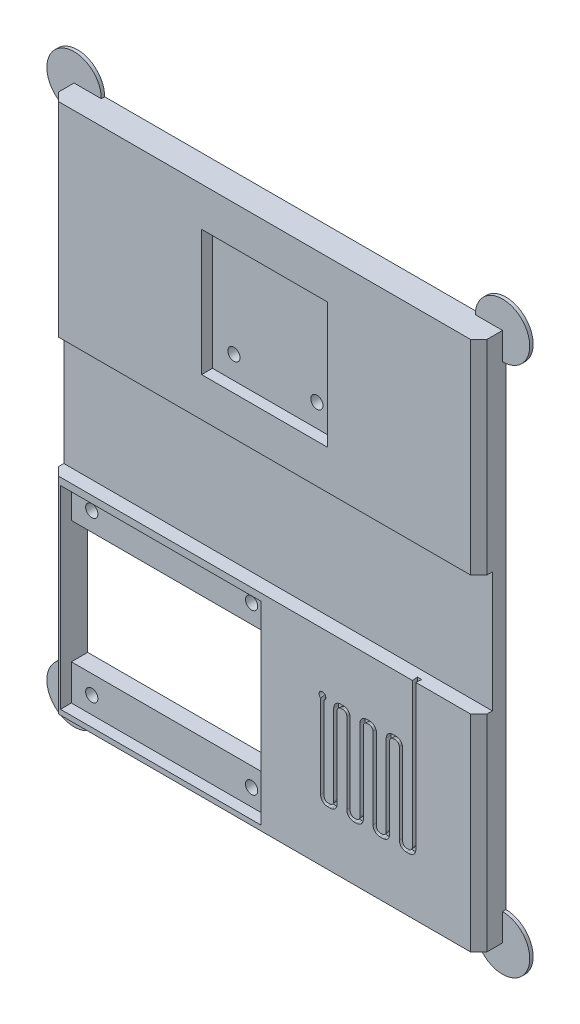
SolidWorks part; units mm, degrees
ref_plane "Front Plane" through (0, 0, 0) normal (0, 0, 1) x (1, 0, 0)
ref_plane "Top Plane" through (0, 0, 0) normal (0, 1, 0) x (1, 0, 0)
ref_plane "Right Plane" through (0, 0, 0) normal (1, 0, 0) x (0, 0, -1)
sketch "Sketch2" [suppressed] plane through (0, 0, 0) normal (0, 0, 1) x (1, 0, 0)
  line L0 (9.8069, 1.0971) -> (9.8069, -3.1704) construction
  line L1 (6.8551, -5.1618) -> (6.8551, -16.1618) construction
  line L2 (6.8551, -16.1618) -> (16.3814, -10.6618) construction
  line L3 (16.3814, -10.6618) -> (6.8551, -5.1618) construction
  line L4 (6.8551, -10.6618) -> (2.6647, -10.6618) construction
  line L5 (9.5069, 1.0971) -> (9.5069, -2.443)
  line L6 (6.5551, -6.3743) -> (6.5551, -9.8618)
  line L7 (8.0551, -15.8154) -> (15.4814, -11.5279)
  line L8 (15.4814, -9.7958) -> (8.0551, -5.5082)
  line L9 (6.0551, -10.3618) -> (3.5127, -10.3618)
  line L10 (10.1069, 1.0971) -> (10.1069, -2.3736)
  line L11 (7.1551, -6.5475) -> (7.1551, -14.7762)
  line L12 (7.9051, -15.2092) -> (15.0314, -11.0948)
  line L13 (15.0314, -10.2288) -> (7.9051, -6.1145)
  line L14 (6.0551, -10.9618) -> (3.5127, -10.9618)
  line L15 (9.5069, 1.0971) -> (9.5069, -3.1704) construction
  line L16 (10.1069, 1.0971) -> (10.1069, -3.1704) construction
  line L17 (6.8551, -10.9618) -> (2.6647, -10.9618) construction
  line L18 (6.8551, -10.3618) -> (2.6647, -10.3618) construction
  line L19 (6.5551, -11.4618) -> (6.5551, -14.9494)
  line L20 (6.5551, -4.6422) -> (6.5551, -16.6814) construction
  line L21 (7.1551, -15.6422) -> (15.7814, -10.6618) construction
  line L22 (15.7814, -10.6618) -> (7.1551, -5.6814) construction
  line L23 (7.1551, -5.6814) -> (7.1551, -15.6422) construction
  line L24 (6.5551, -16.6814) -> (16.9814, -10.6618) construction
  line L25 (16.9814, -10.6618) -> (6.5551, -4.6422) construction
  circle A0 centre (10.1647, -10.6618) radius 7.5 construction
  arc A1 (9.0767, -2.9381) -> (10.5803, -2.8729) centre (10.1647, -10.6618) ccw
  arc A2 (3.0162, -11.5215) -> (3.0162, -9.8021) centre (10.1647, -10.6618) ccw
  arc A3 (9.5069, 1.0971) -> (10.1069, 1.0971) centre (9.8069, 1.0971) cw
  circle A7 centre (10.1647, -10.6618) radius 7.8 construction
  circle A8 centre (10.1647, -10.6618) radius 7.2 construction
  arc A9 (10.1069, -2.3736) -> (10.5803, -2.8729) centre (10.6069, -2.3736) ccw
  arc A10 (9.5069, -2.443) -> (9.0767, -2.9381) centre (9.0069, -2.443) cw
  arc A11 (3.5127, -10.3618) -> (3.0162, -9.8021) centre (3.5127, -9.8618) cw
  arc A12 (3.5127, -10.9618) -> (3.0162, -11.5215) centre (3.5127, -11.4618) ccw
  arc A13 (6.0551, -10.3618) -> (6.5551, -9.8618) centre (6.0551, -9.8618) ccw
  arc A14 (6.5551, -11.4618) -> (6.0551, -10.9618) centre (6.0551, -11.4618) ccw
  arc A15 (15.0314, -11.0948) -> (15.0314, -10.2288) centre (14.7814, -10.6618) ccw
  arc A16 (7.1551, -14.7762) -> (7.9051, -15.2092) centre (7.6551, -14.7762) ccw
  arc A17 (7.1551, -6.5475) -> (7.9051, -6.1145) centre (7.6551, -6.5475) cw
  arc A18 (15.4814, -11.5279) -> (15.4814, -9.7958) centre (14.9814, -10.6618) ccw
  arc A19 (6.5551, -14.9494) -> (8.0551, -15.8154) centre (7.5551, -14.9494) ccw
  arc A20 (6.5551, -6.3743) -> (8.0551, -5.5082) centre (7.5551, -6.3743) cw
  point P12 (6.8551, -10.6618)
  dimension "D2" = 15
  dimension "D3" = 0.5
  dimension "D4" = 1
  dimension "D1" = 11
sketch "Sketch5" plane through (0, 0, 0) normal (0, 0, 1) x (1, 0, 0)
  line L1 (-31.5, 48) -> (31.5, 48)
  line L2 (-31.5, 48) -> (-31.5, -30)
  line L3 (-31.5, -30) -> (31.5, -30)
  line L4 (31.5, 48) -> (31.5, -30)
  point P4 (0, 48)
  dimension "D1" = 63
  dimension "D2" = 30
  dimension "D3" = 48
extrude "Boss-Extrude2" add sketch "Sketch5" along normal blind 4
sketch "Sketch1" plane through (0, 0, 4) normal (0, 0, 1) x (1, 0, 0)
  line L1 (-31, 17.6) -> (31, 17.6) construction
  line L2 (-31, 17.6) -> (-31, 0) construction
  line L3 (-31, 0) -> (31, 0) construction
  line L4 (31, 17.6) -> (31, 0) construction
  line L5 (-9.1, 41.514) -> (9.1, 41.514) construction
  line L6 (-9.1, 41.514) -> (-9.1, 24.114) construction
  line L7 (-9.1, 24.114) -> (9.1, 24.114) construction
  line L8 (9.1, 41.514) -> (9.1, 24.114) construction
  line L9 (-30.1379, -1.3413) -> (-1.1379, -1.3413) construction
  line L10 (-30.1379, -1.3413) -> (-30.1379, -28.8413) construction
  line L11 (-30.1379, -28.8413) -> (-1.1379, -28.8413) construction
  line L12 (-1.1379, -1.3413) -> (-1.1379, -28.8413) construction
  line L13 (-27.6379, -7.8413) -> (-3.6379, -7.8413) construction
  line L14 (-27.6379, -7.8413) -> (-27.6379, -22.8413) construction
  line L15 (-27.6379, -22.8413) -> (-3.6379, -22.8413) construction
  line L16 (-3.6379, -7.8413) -> (-3.6379, -22.8413) construction
  line L17 (0, 37.0153) -> (0, 31.2479) construction
  point P4 (0, 17.6)
  point P18 (0, 0)
  point P20 (-26.7166, -26.6413)
  point P21 (-3.2166, -26.6413)
  point P22 (-3.2166, -4.0013)
  point P23 (-26.7166, -3.1413)
  point P26 (6.1, 27.114)
  point P27 (0, 41.514)
  point P30 (-6.1, 27.114)
  point P32 (-15.6379, -7.8413)
  point P33 (-15.6379, -28.8413)
  dimension "D1" = 17.6
  dimension "D2" = 18.2
  dimension "D3" = 17.4
  dimension "D4" = 27.5
  dimension "D5" = 29
  dimension "D6" = 15
  dimension "D7" = 24
  dimension "D8" = 6
  dimension "D9" = 23.5
  dimension "D10" = 23.5
  dimension "D11" = 12.2
  dimension "D12" = 3
  dimension "D13" = 62
  dimension "D14" = 1.8
sketch "Pause" plane through (0, 0, 4) normal (0, 0, 1) x (1, 0, 0)
  line L0 (19.5, -1.8962) -> (19.5, -8.6557) construction
  line L1 (12.5, -10.5) -> (12.5, -19.5) construction
  line L2 (18.5, -10.5) -> (18.5, -19.5) construction
  line L3 (8, -15) -> (12.5, -15) construction
  line L4 (18.5, -15) -> (23, -15) construction
  line L5 (12.5, -10.5) -> (14.5, -10.5) construction
  line L6 (14.5, -10.5) -> (14.5, -19.5) construction
  line L7 (14.5, -19.5) -> (12.5, -19.5) construction
  line L8 (18.5, -10.5) -> (16.5, -10.5) construction
  line L9 (16.5, -10.5) -> (16.5, -19.5) construction
  line L10 (16.5, -19.5) -> (18.5, -19.5) construction
  line L11 (19.2, -1.8962) -> (19.2, -7.3417)
  line L12 (12.2, -10.9) -> (12.2, -14.2)
  line L13 (14.1, -19.8) -> (12.9, -19.8)
  line L14 (14.8, -10.9) -> (14.8, -19.1)
  line L15 (12.9, -10.2) -> (14.1, -10.2)
  line L16 (18.8, -10.9) -> (18.8, -14.2)
  line L17 (16.9, -19.8) -> (18.1, -19.8)
  line L18 (16.2, -10.9) -> (16.2, -19.1)
  line L19 (18.1, -10.2) -> (16.9, -10.2)
  line L20 (8, -15.3) -> (8.006, -15.3)
  line L21 (19.3, -15.3) -> (22.1521, -15.3)
  line L22 (19.8, -1.8962) -> (19.8, -8.2287)
  line L23 (12.8, -11.3) -> (12.8, -18.7)
  line L24 (13.7, -19.2) -> (13.3, -19.2)
  line L25 (14.2, -11.3) -> (14.2, -18.7)
  line L26 (13.3, -10.8) -> (13.7, -10.8)
  line L27 (18.2, -11.3) -> (18.2, -18.7)
  line L28 (17.3, -19.2) -> (17.7, -19.2)
  line L29 (16.8, -11.3) -> (16.8, -18.7)
  line L30 (17.7, -10.8) -> (17.3, -10.8)
  line L31 (8, -14.7) -> (8.006, -14.7)
  line L32 (19.3, -14.7) -> (22.1521, -14.7)
  line L33 (19.2, -1.8962) -> (19.2, -8.6557) construction
  line L34 (8.8479, -15.3) -> (11.7, -15.3)
  line L35 (19.8, -1.8962) -> (19.8, -8.6557) construction
  line L36 (8, -15.3) -> (12.5, -15.3) construction
  line L37 (8.8479, -14.7) -> (11.7, -14.7)
  line L38 (8, -14.7) -> (12.5, -14.7) construction
  line L39 (12.2, -15.8) -> (12.2, -19.1)
  line L40 (12.2, -10.2) -> (12.2, -19.8) construction
  line L41 (18.5, -14.7) -> (23, -14.7) construction
  line L42 (18.8, -15.8) -> (18.8, -19.1)
  line L43 (18.8, -10.2) -> (18.8, -19.8) construction
  line L44 (18.5, -15.3) -> (23, -15.3) construction
  line L45 (22.994, -14.7) -> (23, -14.7)
  line L46 (22.994, -15.3) -> (23, -15.3)
  line L47 (16.8, -19.2) -> (18.2, -19.2) construction
  line L48 (16.8, -10.8) -> (16.8, -19.2) construction
  line L49 (18.2, -10.8) -> (18.2, -19.2) construction
  line L50 (18.2, -10.8) -> (16.8, -10.8) construction
  line L51 (12.8, -10.8) -> (12.8, -19.2) construction
  line L52 (14.2, -19.2) -> (12.8, -19.2) construction
  line L53 (14.2, -10.8) -> (14.2, -19.2) construction
  line L54 (12.8, -10.8) -> (14.2, -10.8) construction
  line L55 (16.2, -10.2) -> (16.2, -19.8) construction
  line L56 (18.8, -10.2) -> (16.2, -10.2) construction
  line L57 (16.2, -19.8) -> (18.8, -19.8) construction
  line L58 (14.8, -19.8) -> (12.2, -19.8) construction
  line L59 (14.8, -10.2) -> (14.8, -19.8) construction
  line L60 (12.2, -10.2) -> (14.8, -10.2) construction
  line L61 (19.5, -1.8962) -> (19.5, -8.6557) construction
  line L62 (31.5, -30) -> (31.5, 48) construction
  line L64 (-31.5, -30) -> (31.5, -30) construction
  line L65 (19.8, -1.8962) -> (19.2, -1.8962)
  circle A0 centre (15.5, -15) radius 7.5 construction
  arc A2 (18.5072, -7.803) -> (20.0108, -8.6366) centre (15.5, -15) ccw
  arc A3 (8.3515, -15.8597) -> (22.6485, -15.8597) centre (15.5, -15) ccw
  circle A4 centre (15.5, -15) radius 7.8 construction
  circle A5 centre (15.5, -15) radius 7.2 construction
  arc A6 (22.6485, -14.1403) -> (8.3515, -14.1403) centre (15.5, -15) ccw
  arc A7 (19.2, -7.3417) -> (18.5072, -7.803) centre (18.7, -7.3417) cw
  arc A8 (20.0108, -8.6366) -> (19.8, -8.2287) centre (20.3, -8.2287) cw
  arc A9 (8.8479, -15.3) -> (8.3515, -15.8597) centre (8.8479, -15.8) ccw
  arc A10 (8.8479, -14.7) -> (8.3515, -14.1403) centre (8.8479, -14.2) cw
  arc A11 (22.1521, -14.7) -> (22.6485, -14.1403) centre (22.1521, -14.2) ccw
  arc A12 (22.6485, -15.8597) -> (22.1521, -15.3) centre (22.1521, -15.8) ccw
  arc A13 (19.3, -14.7) -> (18.8, -14.2) centre (19.3, -14.2) cw
  arc A14 (19.3, -15.3) -> (18.8, -15.8) centre (19.3, -15.8) ccw
  arc A15 (12.2, -15.8) -> (11.7, -15.3) centre (11.7, -15.8) ccw
  arc A16 (11.7, -14.7) -> (12.2, -14.2) centre (11.7, -14.2) ccw
  arc A17 (17.3, -19.2) -> (16.8, -18.7) centre (17.3, -18.7) cw
  arc A18 (18.2, -18.7) -> (17.7, -19.2) centre (17.7, -18.7) cw
  arc A19 (18.2, -11.3) -> (17.7, -10.8) centre (17.7, -11.3) ccw
  arc A20 (16.8, -11.3) -> (17.3, -10.8) centre (17.3, -11.3) cw
  arc A21 (12.8, -18.7) -> (13.3, -19.2) centre (13.3, -18.7) ccw
  arc A22 (13.7, -19.2) -> (14.2, -18.7) centre (13.7, -18.7) ccw
  arc A23 (14.2, -11.3) -> (13.7, -10.8) centre (13.7, -11.3) ccw
  arc A24 (12.8, -11.3) -> (13.3, -10.8) centre (13.3, -11.3) cw
  arc A25 (16.2, -10.9) -> (16.9, -10.2) centre (16.9, -10.9) cw
  arc A26 (18.8, -10.9) -> (18.1, -10.2) centre (18.1, -10.9) ccw
  arc A27 (18.8, -19.1) -> (18.1, -19.8) centre (18.1, -19.1) cw
  arc A28 (16.9, -19.8) -> (16.2, -19.1) centre (16.9, -19.1) cw
  arc A29 (12.2, -19.1) -> (12.9, -19.8) centre (12.9, -19.1) ccw
  arc A30 (14.1, -19.8) -> (14.8, -19.1) centre (14.1, -19.1) ccw
  arc A31 (14.8, -10.9) -> (14.1, -10.2) centre (14.1, -10.9) ccw
  arc A32 (12.2, -10.9) -> (12.9, -10.2) centre (12.9, -10.9) cw
  point P18 (12.5, -15)
  point P73 (22.6937, -14.7)
  dimension "D5" = 15
  dimension "D6" = 0.5
  dimension "D7" = 0.7
  dimension "D1" = 2
  dimension "D2" = 2
  dimension "D3" = 2
  dimension "D4" = 9
  dimension "D8" = 12
  dimension "D9" = 16
  dimension "D10" = 15
  dimension "D11" = 0.3
  dimension "D12" = 0.3
extrude "Cut-Extrude1" [suppressed] cut sketch "Pause" against normal blind 2
sketch "Teensy" plane through (0, 0, 4) normal (0, 0, 1) x (1, 0, 0)
  line L0 (-31.5, 48) -> (-31.5, -30) construction
  line L1 (-31.5, 18) -> (31.5, 18)
  line L2 (-31.5, 18) -> (-31.5, 0.3)
  line L3 (-31.5, 0.3) -> (31.5, 0.3)
  line L4 (31.5, 18) -> (31.5, 0.3)
  line L5 (31.5, -30) -> (31.5, 48) construction
  line L6 (31.5, 48) -> (-31.5, 48) construction
  dimension "D1" = 17.7
  dimension "D2" = 30
extrude "Cut-Extrude3" cut sketch "Teensy" against normal blind 2
sketch "Sketch7" plane through (0, 0, 4) normal (0, 0, 1) x (1, 0, 0)
  line L1 (-9.25, 42.25) -> (9.25, 42.25)
  line L2 (-9.25, 42.25) -> (-9.25, 23.75)
  line L3 (-9.25, 23.75) -> (9.25, 23.75)
  line L4 (9.25, 42.25) -> (9.25, 23.75)
  line L5 (31.5, 48) -> (-31.5, 48) construction
  point P4 (0, 42.25)
  point P5 (-9.25, 33)
  dimension "D1" = 18.5
  dimension "D2" = 18.5
  dimension "D3" = 15
extrude "Cut-Extrude4" cut sketch "Sketch7" against normal blind 1.6
sketch "Sketch8" plane through (0, 0, 4) normal (0, 0, 1) x (1, 0, 0)
  line L0 (-31.5, -30) -> (31.5, -30) construction
  line L1 (-30, -0.75) -> (-0.5, -0.75)
  line L2 (-30, -0.75) -> (-30, -29.25)
  line L3 (-30, -29.25) -> (-0.5, -29.25)
  line L4 (-0.5, -0.75) -> (-0.5, -29.25)
  line L5 (-31.5, 0.3) -> (-31.5, -30) construction
  point P4 (-30, -15)
  dimension "D1" = 29.5
  dimension "D2" = 28.5
  dimension "D3" = 15
  dimension "D4" = 1.5
extrude "Cut-Extrude5" cut sketch "Sketch8" against normal blind 1.6
sketch "Sketch9" plane through (0, 0, 2.4) normal (0, 0, 1) x (1, 0, 0)
  line L0 (-30, -0.75) -> (-30, -29.25) construction
  line L1 (-30, -6) -> (-1, -6)
  line L2 (-30, -6) -> (-30, -24)
  line L3 (-30, -24) -> (-1, -24)
  line L4 (-1, -6) -> (-1, -24)
  line L5 (-0.5, -0.75) -> (-30, -0.75) construction
  line L6 (-15.25, -0.75) -> (-15.25, -29.25) construction
  line L7 (-18.021, -15) -> (-12.479, -15) construction
  line L8 (-30, -29.25) -> (-0.5, -29.25) construction
  circle A0 centre (-27, -3.25) radius 0.9
  circle A1 centre (-3.5, -3.25) radius 0.9
  circle A2 centre (-3.5, -26.75) radius 0.9
  circle A3 centre (-27, -26.75) radius 0.9
  circle A4 centre (-6.1, 27.114) radius 0.9
  circle A5 centre (6.1, 27.114) radius 0.9
  point P23 (-15.25, -15)
  dimension "D4" = 1.8
  dimension "D1" = 29
  dimension "D2" = 18
  dimension "D5" = 23.5
  dimension "D6" = 23.5
extrude "Cut-Extrude6" cut sketch "Sketch9" against normal through all
sketch "Sketch10" plane through (0, 0, 0) normal (0, 0, -1) x (-1, 0, 0)
  circle A0 centre (31.5, 48) radius 4
  circle A1 centre (-31.5, 48) radius 4
  circle A2 centre (-31.5, -30) radius 4
  circle A3 centre (31.5, -30) radius 4
  dimension "D1" = 8
extrude "Boss-Extrude3" add sketch "Sketch10" against normal blind 0.5
sketch "Sketch11" plane through (0, 0, 4) normal (0, 0, 1) x (1, 0, 0)
  line L0 (-31.5, 48) -> (-31.5, 18) construction
  line L1 (-28.5, 42) -> (-28.1, 42)
  line L2 (-28.5, 42) -> (-28.5, 12)
  line L3 (-28.5, 12) -> (-28.1, 12)
  line L4 (-28.1, 42) -> (-28.1, 12)
  line L5 (-25.5, 42) -> (-24.9, 42)
  line L6 (-25.5, 42) -> (-25.5, 12)
  line L7 (-25.5, 12) -> (-24.9, 12)
  line L8 (-24.9, 42) -> (-24.9, 12)
  line L9 (-22.5, 42) -> (-21.7, 42)
  line L10 (-22.5, 42) -> (-22.5, 12)
  line L11 (-22.5, 12) -> (-21.7, 12)
  line L12 (-21.7, 42) -> (-21.7, 12)
  line L13 (31.5, 48) -> (-31.5, 48) construction
  dimension "D1" = 30
  dimension "D2" = 3
  dimension "D3" = 3
  dimension "D4" = 3
  dimension "D5" = 0.4
  dimension "D6" = 0.6
  dimension "D7" = 0.8
  dimension "D8" = 6
extrude "Cut-Extrude7" [suppressed] cut sketch "Sketch11" against normal blind 2 draft 5
chamfer "Chamfer2" distance 1.2 angle 45 4 edges at (-31.5, -14.85, 4) (31.5, -14.85, 4) (31.5, 33, 4) (-31.5, 33, 4)
sketch "Sketch12" plane through (0, 0, 4) normal (0, 0, 1) x (1, 0, 0)
  line L0 (22, 0.3) -> (22, -21.75) construction
  line L1 (22, -21.75) -> (20.0714, -21.75) construction
  line L2 (20.0714, -21.75) -> (20.0714, -8.25) construction
  line L3 (20.0714, -8.25) -> (18.1429, -8.25) construction
  line L4 (18.1429, -8.25) -> (18.1429, -21.75) construction
  line L5 (18.1429, -21.75) -> (16.2143, -21.75) construction
  line L6 (16.2143, -21.75) -> (16.2143, -8.25) construction
  line L7 (16.2143, -8.25) -> (14.2857, -8.25) construction
  line L8 (14.2857, -8.25) -> (14.2857, -21.75) construction
  line L9 (14.2857, -21.75) -> (12.3571, -21.75) construction
  line L10 (12.3571, -21.75) -> (12.3571, -8.25) construction
  line L11 (12.3571, -8.25) -> (10.4286, -8.25) construction
  line L12 (10.4286, -8.25) -> (10.4286, -21.75) construction
  line L13 (10.4286, -21.75) -> (8.5, -21.75) construction
  line L14 (21.75, 0.3) -> (21.75, -20.9)
  line L15 (21.15, -21.5) -> (20.9214, -21.5)
  line L16 (20.3214, -20.9) -> (20.3214, -9)
  line L17 (19.3214, -8) -> (18.8929, -8)
  line L18 (8.5, -21.75) -> (8.5, -8.25) construction
  line L19 (31.5, -26) -> (31.5, 44) construction
  line L20 (-27.5, -30) -> (27.5, -30) construction
  line L21 (-31.5, 0.3) -> (31.5, 0.3) construction
  line L22 (17.8929, -9) -> (17.8929, -20.9)
  line L23 (17.2929, -21.5) -> (17.0643, -21.5)
  line L24 (16.4643, -20.9) -> (16.4643, -9)
  line L25 (15.4643, -8) -> (15.0357, -8)
  line L26 (14.0357, -9) -> (14.0357, -20.9)
  line L27 (13.4357, -21.5) -> (13.2071, -21.5)
  line L28 (12.6071, -20.9) -> (12.6071, -9)
  line L29 (11.6071, -8) -> (11.1786, -8)
  line L30 (10.1786, -9) -> (10.1786, -20.9)
  line L31 (9.5786, -21.5) -> (9.35, -21.5)
  line L32 (8.75, -20.9) -> (8.75, -8.25)
  line L33 (22.25, 0.3) -> (22.25, -21)
  line L34 (21.25, -22) -> (20.8214, -22)
  line L35 (19.8214, -21) -> (19.8214, -9.1)
  line L36 (19.2214, -8.5) -> (18.9929, -8.5)
  line L37 (18.3929, -9.1) -> (18.3929, -21)
  line L38 (17.3929, -22) -> (16.9643, -22)
  line L39 (15.9643, -21) -> (15.9643, -9.1)
  line L40 (15.3643, -8.5) -> (15.1357, -8.5)
  line L41 (14.5357, -9.1) -> (14.5357, -21)
  line L42 (13.5357, -22) -> (13.1071, -22)
  line L43 (12.1071, -21) -> (12.1071, -9.1)
  line L44 (11.5071, -8.5) -> (11.2786, -8.5)
  line L45 (10.6786, -9.1) -> (10.6786, -21)
  line L46 (9.6786, -22) -> (9.25, -22)
  line L47 (8.25, -21) -> (8.25, -8.25)
  line L48 (21.75, 0.3) -> (22.25, 0.3)
  line L49 (8.75, -8.25) -> (8.25, -8.25)
  line L50 (14.0357, -21.5) -> (12.6071, -21.5) construction
  line L51 (12.6071, -21.5) -> (12.6071, -8) construction
  line L52 (14.0357, -8) -> (14.0357, -21.5) construction
  line L53 (17.8929, -21.5) -> (16.4643, -21.5) construction
  line L54 (16.4643, -21.5) -> (16.4643, -8) construction
  line L55 (17.8929, -8) -> (17.8929, -21.5) construction
  line L56 (21.75, -21.5) -> (20.3214, -21.5) construction
  line L57 (20.3214, -21.5) -> (20.3214, -8) construction
  line L58 (21.75, 0.3) -> (21.75, -21.5) construction
  line L59 (19.8214, -22) -> (19.8214, -8.5) construction
  line L60 (19.8214, -8.5) -> (18.3929, -8.5) construction
  line L61 (18.3929, -8.5) -> (18.3929, -22) construction
  line L62 (15.9643, -22) -> (15.9643, -8.5) construction
  line L63 (15.9643, -8.5) -> (14.5357, -8.5) construction
  line L64 (14.5357, -8.5) -> (14.5357, -22) construction
  line L65 (12.1071, -22) -> (12.1071, -8.5) construction
  line L66 (12.1071, -8.5) -> (10.6786, -8.5) construction
  line L67 (10.6786, -8.5) -> (10.6786, -22) construction
  line L68 (10.1786, -8) -> (10.1786, -21.5) construction
  line L69 (10.1786, -21.5) -> (8.75, -21.5) construction
  line L70 (8.75, -21.5) -> (8.75, -8.25) construction
  line L71 (12.6071, -8) -> (10.1786, -8) construction
  line L72 (16.4643, -8) -> (14.0357, -8) construction
  line L73 (20.3214, -8) -> (17.8929, -8) construction
  line L74 (22.25, 0.3) -> (22.25, -22) construction
  line L75 (22.25, -22) -> (19.8214, -22) construction
  line L76 (18.3929, -22) -> (15.9643, -22) construction
  line L77 (14.5357, -22) -> (12.1071, -22) construction
  line L78 (10.6786, -22) -> (8.25, -22) construction
  line L79 (8.25, -22) -> (8.25, -8.25) construction
  arc A0 (13.2071, -21.5) -> (12.6071, -20.9) centre (13.2071, -20.9) cw
  arc A1 (14.0357, -20.9) -> (13.4357, -21.5) centre (13.4357, -20.9) cw
  arc A2 (17.0643, -21.5) -> (16.4643, -20.9) centre (17.0643, -20.9) cw
  arc A3 (17.8929, -20.9) -> (17.2929, -21.5) centre (17.2929, -20.9) cw
  arc A4 (20.9214, -21.5) -> (20.3214, -20.9) centre (20.9214, -20.9) cw
  arc A5 (21.75, -20.9) -> (21.15, -21.5) centre (21.15, -20.9) cw
  arc A6 (19.8214, -9.1) -> (19.2214, -8.5) centre (19.2214, -9.1) ccw
  arc A7 (18.9929, -8.5) -> (18.3929, -9.1) centre (18.9929, -9.1) ccw
  arc A8 (15.9643, -9.1) -> (15.3643, -8.5) centre (15.3643, -9.1) ccw
  arc A9 (15.1357, -8.5) -> (14.5357, -9.1) centre (15.1357, -9.1) ccw
  arc A10 (12.1071, -9.1) -> (11.5071, -8.5) centre (11.5071, -9.1) ccw
  arc A11 (11.2786, -8.5) -> (10.6786, -9.1) centre (11.2786, -9.1) ccw
  arc A12 (10.1786, -20.9) -> (9.5786, -21.5) centre (9.5786, -20.9) cw
  arc A13 (9.35, -21.5) -> (8.75, -20.9) centre (9.35, -20.9) cw
  arc A14 (11.1786, -8) -> (10.1786, -9) centre (11.1786, -9) ccw
  arc A15 (12.6071, -9) -> (11.6071, -8) centre (11.6071, -9) ccw
  arc A16 (15.0357, -8) -> (14.0357, -9) centre (15.0357, -9) ccw
  arc A17 (16.4643, -9) -> (15.4643, -8) centre (15.4643, -9) ccw
  arc A18 (18.8929, -8) -> (17.8929, -9) centre (18.8929, -9) ccw
  arc A19 (20.3214, -9) -> (19.3214, -8) centre (19.3214, -9) ccw
  arc A20 (22.25, -21) -> (21.25, -22) centre (21.25, -21) cw
  arc A21 (20.8214, -22) -> (19.8214, -21) centre (20.8214, -21) cw
  arc A22 (18.3929, -21) -> (17.3929, -22) centre (17.3929, -21) cw
  arc A23 (16.9643, -22) -> (15.9643, -21) centre (16.9643, -21) cw
  arc A24 (14.5357, -21) -> (13.5357, -22) centre (13.5357, -21) cw
  arc A25 (13.1071, -22) -> (12.1071, -21) centre (13.1071, -21) cw
  arc A26 (10.6786, -21) -> (9.6786, -22) centre (9.6786, -21) cw
  arc A27 (9.25, -22) -> (8.25, -21) centre (9.25, -21) cw
  point P22 (8.5, -15)
  dimension "D5" = 0.6
  dimension "D6" = 1
  dimension "D1" = 13.5
  dimension "D2" = 13.5
  dimension "D3" = 9.5
  dimension "D4" = 15
  dimension "D7" = 0.25
  dimension "D8" = 0.25
extrude "Cut-Extrude8" cut sketch "Sketch12" against normal blind 0.8 draft 5 draft outward yes
sketch "Sketch13" plane through (0, 0, 4) normal (0, 0, 1) x (1, 0, 0)
  line L0 (8.75, -8.25) -> (8.25, -8.25) construction
  circle A0 centre (8.5172, -8.25) radius 0.5
  dimension "D1" = 1
extrude "Cut-Extrude9" cut sketch "Sketch13" against normal through all
